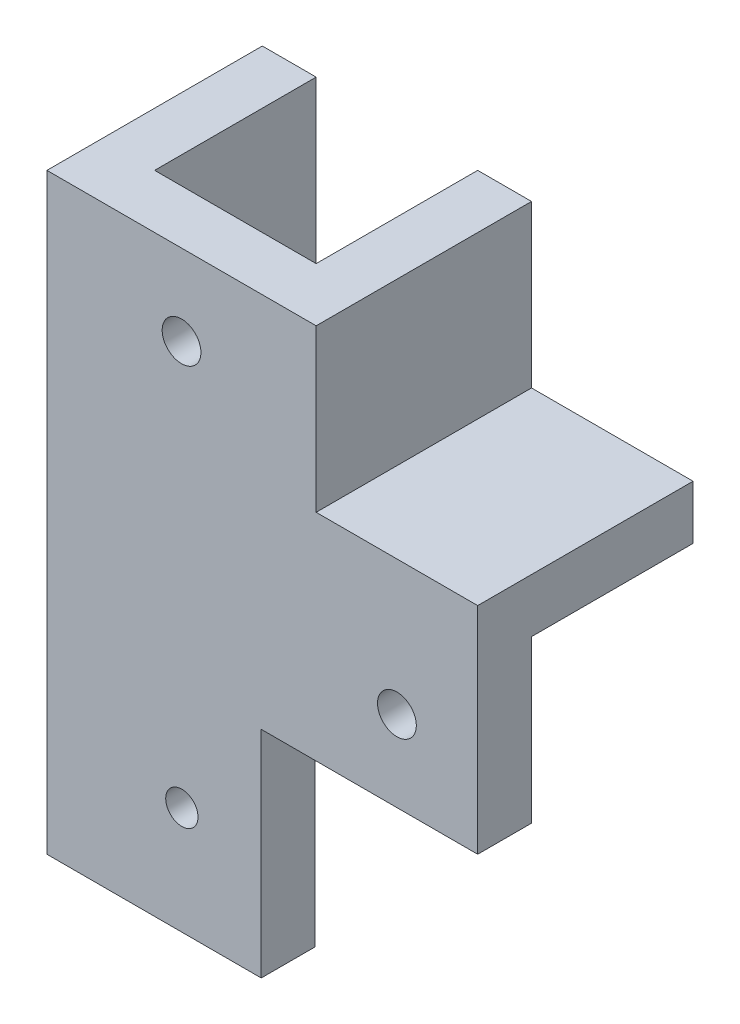
SolidWorks part; units mm, degrees
ref_plane "前视基准面" through (0, 0, 0) normal (0, 0, 1) x (1, 0, 0)
ref_plane "上视基准面" through (0, 0, 0) normal (0, 1, 0) x (1, 0, 0)
ref_plane "右视基准面" through (0, 0, 0) normal (1, 0, 0) x (0, 0, -1)
sketch "Sketch1" plane through (0, 0, 0) normal (0, 0, 1) x (1, 0, 0)
  line L0 (7.3701, -25.8068) -> (27.4701, -25.8068)
  line L3 (-7.5299, 9.1932) -> (7.4701, 9.1932)
  line L4 (-7.5299, 9.1932) -> (-7.5299, -25.8068)
  line L6 (7.4701, 9.1932) -> (7.4701, -10.8068)
  line L7 (27.4701, -25.8068) -> (27.4701, -10.8068)
  line L8 (27.4701, -10.8068) -> (7.4701, -10.8068)
  line L12 (-7.5299, -25.8068) -> (7.3701, -25.8068)
  dimension "D1" = 15
  dimension "D2" = 35
  dimension "D3" = 35
  dimension "D4" = 15
extrude "Boss-Extrude1" add sketch "Sketch1" along normal blind 5
sketch "Sketch2" plane through (0, 0, 0) normal (0, 0, -1) x (-1, 0, 0)
  line L0 (-7.4701, 9.1932) -> (-12.4701, 9.1932)
  line L1 (-12.4701, 9.1932) -> (-12.4701, -5.8068)
  line L2 (-12.4701, -5.8068) -> (-27.4701, -5.8068)
  line L3 (-27.4701, -10.8068) -> (-27.4701, -5.8068)
  line L4 (-27.4701, -10.8068) -> (-7.4701, -10.8068)
  line L5 (-7.4701, -10.8068) -> (-7.4701, 9.1932)
  dimension "D1" = 5
  dimension "D2" = 5
extrude "Boss-Extrude2" add sketch "Sketch2" along normal blind 15 separate body
sketch "Sketch3" plane through (0, 0, 0) normal (0, 0, -1) x (-1, 0, 0)
  line L0 (7.5299, 9.1932) -> (12.5299, 9.1932)
  line L2 (12.5299, -45.8068) -> (12.5299, 9.1932)
  line L3 (7.5299, -25.8068) -> (7.5299, 9.1932)
  line L5 (7.5299, -25.8068) -> (7.5299, -45.8068)
  line L6 (7.5299, -45.8068) -> (12.5299, -45.8068)
  dimension "D1" = 5
  dimension "D2" = 55
extrude "Boss-Extrude3" add sketch "Sketch3" along normal blind 15 separate body
sketch "Sketch4" plane through (0, 0, 0) normal (0, 0, -1) x (-1, 0, 0)
  line L0 (-27.4701, -10.8068) -> (-7.4701, -10.8068) construction
  line L1 (-27.4701, -25.8068) -> (-27.4701, -10.8068) construction
  line L2 (-7.4701, -10.8068) -> (-7.4701, 9.1932) construction
  line L3 (-7.4701, 9.1932) -> (7.5299, 9.1932) construction
  circle A0 centre (0.0299, 1.6932) radius 1.8
  circle A1 centre (-19.9701, -18.3068) radius 1.8
  dimension "D1" = 3.6
  dimension "D2" = 3.6
  dimension "D3" = 7.5
  dimension "D4" = 7.5
  dimension "D5" = 7.5
  dimension "D6" = 7.5
extrude "Cut-Extrude1" cut sketch "Sketch4" against normal through all
sketch "Sketch6" plane through (0, 0, 5) normal (0, 0, 1) x (1, 0, 0)
  line L0 (-7.5299, -25.8068) -> (-7.5299, -45.8068)
  line L1 (-7.5299, -25.8068) -> (27.4701, -25.8068) construction
  line L2 (-7.5299, -45.8068) -> (7.3701, -45.8068)
  line L3 (7.3701, -45.8068) -> (7.3701, -25.8068)
  line L4 (7.3701, -25.8068) -> (-7.5299, -25.8068)
  dimension "D1" = 14.9
  dimension "D2" = 20
extrude "Boss-Extrude4" add sketch "Sketch6" against normal blind 5
sketch "Sketch8" plane through (0, 0, 5) normal (0, 0, 1) x (1, 0, 0)
  line L0 (-7.5299, -45.8068) -> (7.3701, -45.8068) construction
  circle A0 centre (0, -35.8068) radius 1.5
  dimension "D1" = 3
  dimension "D2" = 10
extrude "Cut-Extrude3" cut sketch "Sketch8" against normal through all contours A0
sketch "Sketch9" plane through (0, 0, 5) normal (0, 0, 1) x (1, 0, 0)
  line L1 (-12.5299, 9.1932) -> (-7.5299, 9.1932)
  line L2 (-12.5299, 9.1932) -> (-12.5299, -45.8068)
  line L3 (-12.5299, -45.8068) -> (-7.5299, -45.8068)
  line L4 (-7.5299, 9.1932) -> (-7.5299, -45.8068)
extrude "Boss-Extrude5" add sketch "Sketch9" against normal blind 5
sketch "Sketch10" plane through (0, 0, 0) normal (0, 0, 1) x (1, 0, 0)
  line L0 (7.4701, 9.1932) -> (12.4701, 9.1932)
  line L1 (7.4701, 9.1932) -> (12.4701, 9.1932) construction
  line L2 (12.4701, 9.1932) -> (12.4701, -5.8068)
  line L3 (12.4701, -5.8068) -> (27.4701, -5.8068)
  line L4 (12.4701, -5.8068) -> (27.4701, -5.8068) construction
  line L5 (27.4701, -5.8068) -> (27.4701, -10.8068) construction
  line L6 (27.4701, -5.8068) -> (27.4701, -10.8068)
  line L7 (27.4701, -10.8068) -> (7.4701, -10.8068)
  line L8 (7.4701, -10.8068) -> (7.4701, 9.1932)
extrude "Boss-Extrude6" add sketch "Sketch10" along normal blind 5
